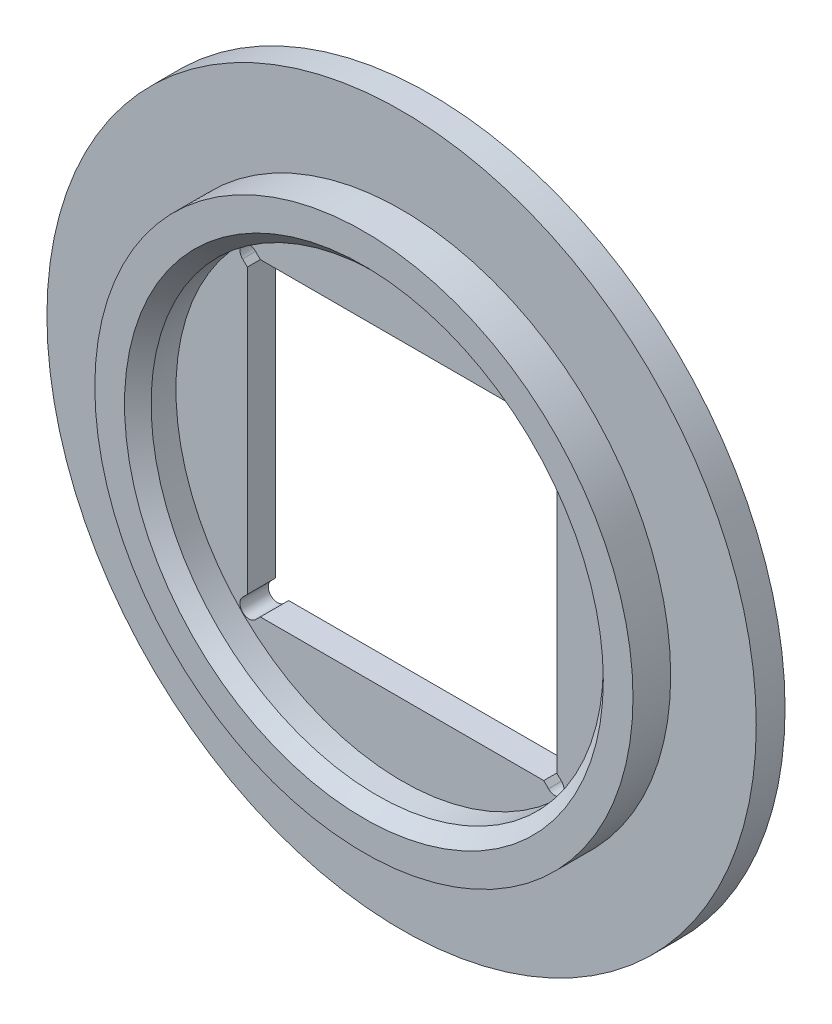
SolidWorks part; units mm, degrees
ref_plane "前视基准面" through (0, 0, 0) normal (0, 0, 1) x (1, 0, 0)
ref_plane "上视基准面" through (0, 0, 0) normal (0, 1, 0) x (1, 0, 0)
ref_plane "右视基准面" through (0, 0, 0) normal (1, 0, 0) x (0, 0, -1)
sketch "草图1" plane through (0, 0, 0) normal (0, 0, 1) x (1, 0, 0)
  circle A0 centre (0, 0) radius 8
extrude "凸台-拉伸1" add sketch "草图1" along normal blind 0.65
sketch "草图2" plane through (0, 0, 0) normal (0, 0, 1) x (1, 0, 0)
  circle A0 centre (0, 0) radius 6.07
  circle A1 centre (0, 0) radius 5.1
extrude "凸台-拉伸2" add sketch "草图2" along normal blind 0.85 from surface at 0.65 starting at face at (8, 0, 0.65)
sketch "草图3" plane through (0, 0, 0) normal (0, 0, 1) x (1, 0, 0)
  circle A0 centre (0, 0) radius 5.1
extrude "切除-拉伸1" cut sketch "草图3" against normal blind 0.01 from surface at 0.65 starting at face at (6.07, 0, 0.65)
sketch "草图4" plane through (0, 0, 0) normal (0, 0, 1) x (1, 0, 0)
  line L28 (-3.49, 0) -> (-3.49, 3.49)
  line L29 (-3.49, 3.49) -> (3.49, 3.49)
  line L30 (3.49, 3.49) -> (3.49, -3.49)
  line L31 (3.49, -3.49) -> (-3.49, -3.49)
  line L32 (-3.49, -3.49) -> (-3.49, 0)
extrude "切除-拉伸2" cut sketch "草图4" along normal up to surface (0.64 mm away) up to face at (5.1, 0, 0.64)
chamfer "倒角1" distance 0.3 angle 45 1 edges at (5.1, 0, 1.5)
sketch "草图6" plane through (0, 0, 0) normal (0, 0, 1) x (1, 0, 0)
  circle A1 centre (-3.45, 3.45) radius 0.2074
  circle A2 centre (3.45, 3.45) radius 0.2074
  circle A3 centre (3.45, -3.45) radius 0.2074
  circle A4 centre (-3.45, -3.45) radius 0.2074
extrude "切除-拉伸3" cut sketch "草图6" along normal up to surface (0.64 mm away) from surface at 0 up to face at (0, 0, 0.64) starting at face at (8, 0, 0)
sketch "草图7" plane through (0, 0, 0) normal (0, 0, 1) x (1, 0, 0)
  line L0 (-3.45, 3.45) -> (-3.5966, 3.3034)
  line L1 (-3.45, 3.45) -> (-3.3034, 3.5966)
  line L2 (-3.5966, 3.3034) -> (-3.1264, 2.8332)
  line L4 (-3.3034, 3.5966) -> (-2.8332, 3.1264)
  line L5 (-2.8332, 3.1264) -> (-3.1264, 2.8332)
  line L7 (2.8332, 3.1264) -> (3.1264, 2.8332)
  line L8 (3.3034, 3.5966) -> (2.8332, 3.1264)
  line L9 (3.5966, 3.3034) -> (3.1264, 2.8332)
  line L10 (3.45, 3.45) -> (3.3034, 3.5966)
  line L11 (3.45, 3.45) -> (3.5966, 3.3034)
  line L13 (3.45, -3.45) -> (3.5966, -3.3034)
  line L14 (3.45, -3.45) -> (3.3034, -3.5966)
  line L15 (3.5966, -3.3034) -> (3.1264, -2.8332)
  line L16 (3.3034, -3.5966) -> (2.8332, -3.1264)
  line L17 (2.8332, -3.1264) -> (3.1264, -2.8332)
  line L18 (-2.8332, -3.1264) -> (-3.1264, -2.8332)
  line L19 (-3.3034, -3.5966) -> (-2.8332, -3.1264)
  line L20 (-3.5966, -3.3034) -> (-3.1264, -2.8332)
  line L21 (-3.45, -3.45) -> (-3.3034, -3.5966)
  line L22 (-3.45, -3.45) -> (-3.5966, -3.3034)
  arc A1 (-3.2465, 3.49) -> (-3.49, 3.2465) centre (-3.45, 3.45) ccw construction
extrude "切除-拉伸4" cut sketch "草图7" along normal up to surface (0.64 mm away) from surface at 0 up to face at (0, 0, 0.64) starting at face at (0, 0, 0)
